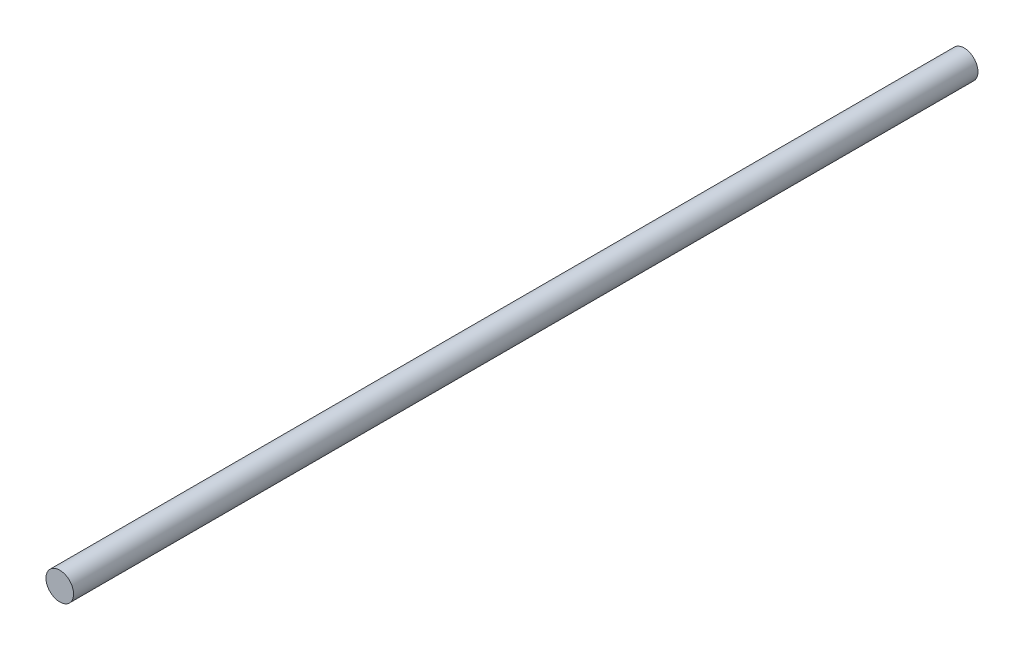
SolidWorks part; units mm, degrees
material "Литая легированная сталь"
ref_plane "Спереди" through (0, 0, 0) normal (0, 0, 1) x (1, 0, 0)
ref_plane "Сверху" through (0, 0, 0) normal (0, 1, 0) x (1, 0, 0)
ref_plane "Справа" through (0, 0, 0) normal (1, 0, 0) x (0, 0, -1)
sketch "Эскиз1" plane through (0, 0, 0) normal (0, 0, 1) x (1, 0, 0)
  circle A0 centre (0, 0) radius 5
  dimension "D1" = 10
extrude "Бобышка-Вытянуть1" add sketch "Эскиз1" along normal blind 328
